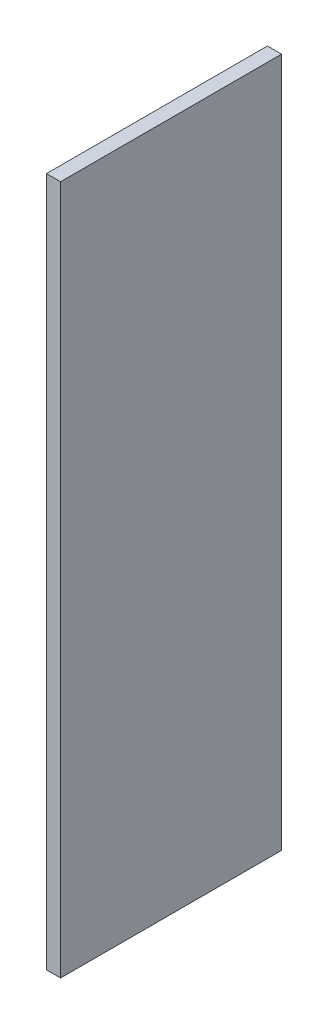
SolidWorks part; units mm, degrees
ref_plane "Спереди" through (0, 0, 0) normal (0, 0, 1) x (1, 0, 0)
ref_plane "Сверху" through (0, 0, 0) normal (0, 1, 0) x (1, 0, 0)
ref_plane "Справа" through (0, 0, 0) normal (1, 0, 0) x (0, 0, -1)
sketch "Эскиз1" plane through (0, 0, 0) normal (1, 0, 0) x (0, 0, -1)
  line L1 (141, 440) -> (-141, 440)
  line L2 (141, 440) -> (141, -440)
  line L3 (141, -440) -> (-141, -440)
  line L4 (-141, 440) -> (-141, -440)
  line L5 (141, 440) -> (-141, -440) construction
  line L6 (141, -440) -> (-141, 440) construction
  point P0 (0, 0)
  dimension "D1" = 880
  dimension "D2" = 282
extrude "Бобышка-Вытянуть1" add sketch "Эскиз1" along normal blind 18
